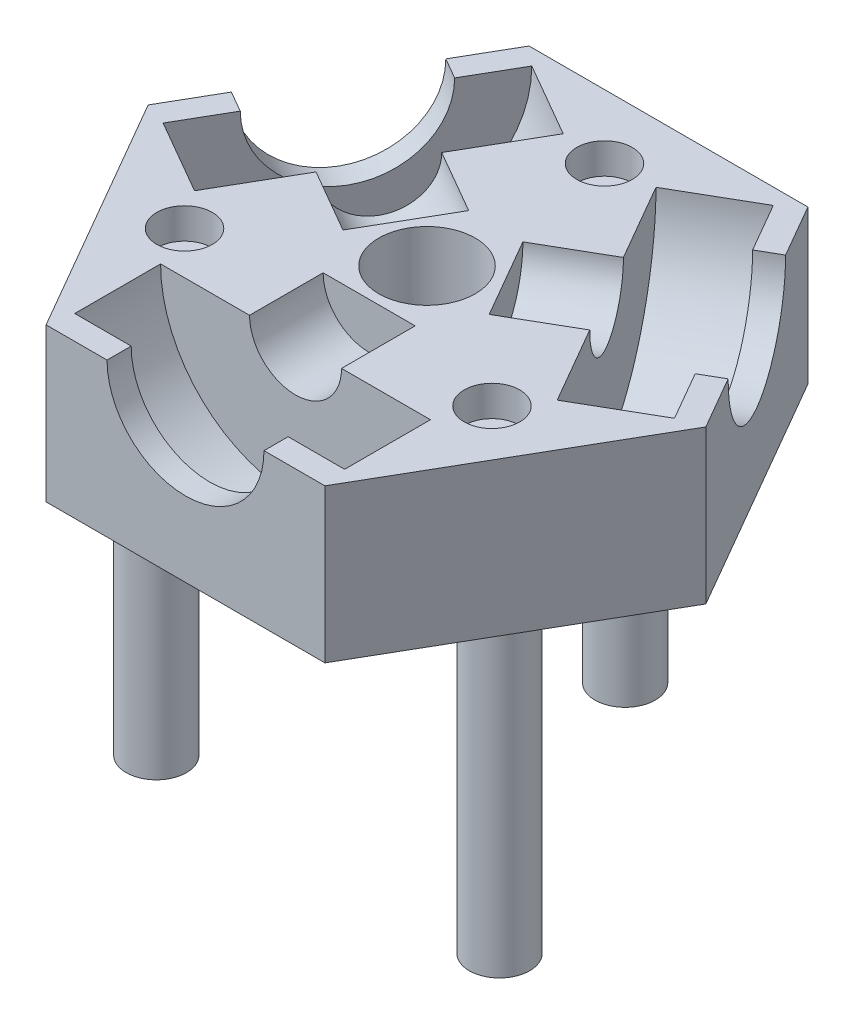
SolidWorks part; units mm, degrees
ref_plane "Front Plane" through (0, 0, 0) normal (0, 0, 1) x (1, 0, 0)
ref_plane "Top Plane" through (0, 0, 0) normal (0, 1, 0) x (1, 0, 0)
ref_plane "Right Plane" through (0, 0, 0) normal (1, 0, 0) x (0, 0, -1)
sketch "Sketch1" plane through (0, 0, 0) normal (0, 1, 0) x (1, 0, 0)
  line L1 (11.547, -20) -> (23.094, 0)
  line L2 (23.094, 0) -> (11.547, 20)
  line L3 (11.547, 20) -> (-11.547, 20)
  line L4 (-11.547, 20) -> (-23.094, 0)
  line L5 (-23.094, 0) -> (-11.547, -20)
  line L6 (-11.547, -20) -> (11.547, -20)
  circle A0 centre (0, 0) radius 20 construction
  dimension "D1" = 40
extrude "Boss-Extrude1" add sketch "Sketch1" along normal blind 12.7 contours L4 L5 L6 L1 L2 L3
sketch "Sketch2" plane through (0, 0, 0) normal (0, -1, 0) x (1, 0, 0)
  circle A0 centre (0, 0) radius 4.1
  circle A1 centre (0, 0) radius 5.5
  dimension "D1" = 8.2
  dimension "D2" = 11
extrude "Boss-Extrude2" add sketch "Sketch2" along normal blind 3.5
sketch "Sketch5" plane through (0, 12.7, 0) normal (0, 1, 0) x (1, 0, 0)
  line L14 (0, -20) -> (0, -4.792)
  line L15 (-11.547, -20) -> (11.547, -20) construction
  line L16 (0, -4.792) -> (-3.81, -4.792)
  line L17 (-3.81, -4.792) -> (-3.81, -10.888)
  line L18 (-3.81, -10.888) -> (-11.176, -10.888)
  line L19 (-11.176, -10.888) -> (-11.176, -18)
  line L20 (-11.176, -18) -> (-6.5, -18)
  line L21 (-6.5, -18) -> (-6.5, -20)
  line L22 (-6.5, -20) -> (0, -20)
  dimension "D1" = 6.5
  dimension "D2" = 11.176
  dimension "D3" = 2
  dimension "D4" = 7.112
  dimension "D5" = 6.096
  dimension "D6" = 3.81
revolve "Cut-Revolve1" cut sketch "Sketch5" angle 360 about L14
pattern_circular "CirPattern1" count 3 over 360 about axis through (0, 0, 0) along (0, 1, 0) of "Cut-Revolve1"
sketch "Sketch6" plane through (0, 12.7, 0) normal (0, 1, 0) x (1, 0, 0)
  circle A0 centre (0, 0) radius 4
  dimension "D1" = 8
extrude "Cut-Extrude1" cut sketch "Sketch6" against normal through all
sketch "Random Circles" plane through (0, 12.7, 0) normal (0, 1, 0) x (1, 0, 0)
  line L0 (11.547, 20) -> (-11.547, 20) construction
  line L1 (-23.094, 0) -> (-11.547, -20) construction
  line L2 (11.547, -20) -> (23.094, 0) construction
  circle A0 centre (0, 14.7) radius 2.3
  circle A1 centre (12.7306, -7.35) radius 2.3
  circle A2 centre (-12.7306, -7.35) radius 2.3
  point P11 (0, 0)
  dimension "D1" = 4.6
  dimension "D2" = 3
  dimension "D4" = 3
  dimension "D5" = 3
  dimension "D3" = 3
sketch "Sketch8" plane through (0, 0, 0) normal (0, 1, 0) x (1, 0, 0)
  line L0 (11.547, 20) -> (-11.547, 20) construction
  line L2 (11.547, -20) -> (23.094, 0) construction
  line L4 (-23.094, 0) -> (-11.547, -20) construction
  circle A0 centre (0, 16.4096) radius 2.5
  circle A3 centre (14.2111, -8.2048) radius 2.5
  circle A4 centre (-14.2111, -8.2048) radius 2.5
  point P11 (0, 0)
  point P12 (0, 0)
  dimension "D1" = 5
  dimension "D2" = 16.4096
  dimension "D6" = 3
  dimension "D4" = 3.5904
  dimension "D3" = 3.5904
  dimension "D5" = 3.5904
extrude "Cut-Extrude2" cut sketch "Random Circles" against normal blind 2.54
extrude "Boss-Extrude3" add sketch "Sketch8" against normal blind 25.4
